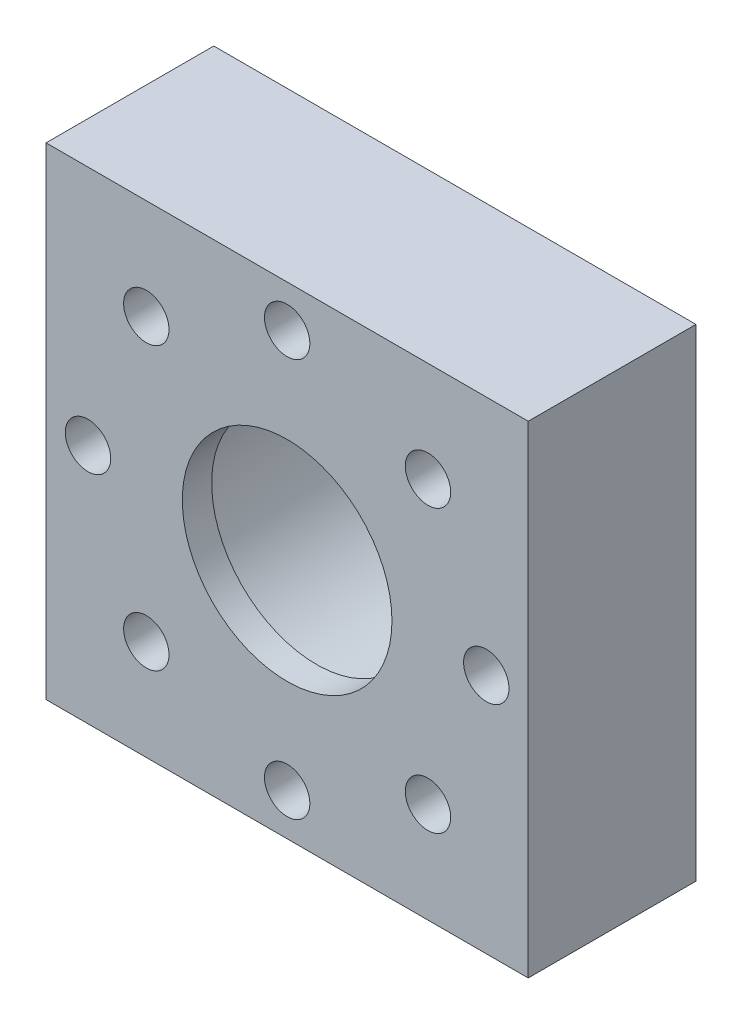
SolidWorks part; units mm, degrees
ref_plane "Front Plane" through (0, 0, 0) normal (0, 0, 1) x (1, 0, 0)
ref_plane "Top Plane" through (0, 0, 0) normal (0, 1, 0) x (1, 0, 0)
ref_plane "Right Plane" through (0, 0, 0) normal (1, 0, 0) x (0, 0, -1)
sketch "Sketch1" plane through (0, 0, 0) normal (0, 0, 1) x (1, 0, 0)
  line L0 (0, 0) -> (29.21, 0) construction
  line L1 (-29.21, -29.21) -> (29.21, -29.21)
  line L2 (-29.21, -29.21) -> (-29.21, 29.21)
  line L3 (-29.21, 29.21) -> (29.21, 29.21)
  line L4 (29.21, -29.21) -> (29.21, 29.21)
  line L5 (0, 0) -> (0, 29.21) construction
  dimension "D1" = 58.42
extrude "Boss-Extrude1" add sketch "Sketch1" along normal blind 20.32
sketch "Sketch5" plane through (0, 0, 0) normal (0, 0, -1) x (-1, 0, 0)
  point P0 (0, 0)
sketch "Sketch6" plane through (0, 0, 0) normal (0, 0, -1) x (-1, 0, 0)
  circle A0 centre (0, 0) radius 29.21 construction
  circle A1 centre (0, 0) radius 24.13 construction
  point P5 (0, 24.13)
  dimension "D1" = 58.42
  dimension "D2" = 5.08
hole_wizard "1 NPT Tapped Hole2" positions "Sketch5" profile "Sketch7" size "1" standard "ANSI Inch" end condition up to next
sketch "Sketch7" plane through (0, 0, 0) normal (1, 0, 0) x (0, 1, 0)
  line L0 (0, 0) -> (0, 20.32)
  line L1 (0, 20.32) -> (14.4907, 20.32)
  line L2 (-15.228, 16.764) -> (-15.7299, 0) construction
  line L3 (14.4907, 20.32) -> (14.4907, 16.764)
  line L4 (14.4907, 16.764) -> (15.228, 16.764)
  line L5 (15.228, 16.764) -> (15.7299, 0)
  line L7 (15.7299, 0) -> (0, 0)
  line L8 (0, -6.35) -> (0, 107.95) construction
  line L11 (-14.4907, 16.764) -> (-15.228, 16.764) construction
  dimension "Thru Tap Drill Dia." = 28.9814
  dimension "Thru Tap Drill Depth" = 20.32
  dimension "Thread Dia." = 31.4598
  dimension "Thread Angle" = 3.43
  dimension "Thread Depth" = 16.764
cosmetic thread "Hole Thread1" parameters "D1"=16.764, "D2"=33.3996
hole_wizard "M5 Clearance Hole1" positions "Sketch6" profile "Sketch8" hole size "M5" standard "ANSI Metric" end condition up to next
sketch "Sketch8" plane through (0, 24.13, 0) normal (1, 0, 0) x (0, 1, 0)
  line L0 (0, 0) -> (0, 20.32)
  line L1 (0, 20.32) -> (2.75, 20.32)
  line L2 (2.75, 20.32) -> (2.75, 0)
  line L5 (2.75, 0) -> (0, 0)
  line L11 (0, -6.35) -> (0, 107.95) construction
  dimension "Thru Hole Dia." = 5.5
  dimension "Thru Hole Depth" = 20.32
pattern_circular "CirPattern1" count 8 every 45 about axis through (0, 0, 0) along (0, 0, 1) of "M5 Clearance Hole1"
sketch "Sketch9" plane through (0, 0, 20.32) normal (0, 0, 1) x (1, 0, 0)
  circle A0 centre (0, 0) radius 12.7
  circle A1 centre (0, 0) radius 14.4907 construction
  circle A2 centre (0, 0) radius 14.4907
  dimension "D1" = 25.4
extrude "Boss-Extrude2" add sketch "Sketch9" against normal up to surface (3.556 mm away) up to face at (-14.4907, 0, 16.764)
equation "\"le\"=2.43593"
equation "\"Cavity_Depth\" = 0.031in"
equation "\"Cavity_Width\" = 0.031in"
equation "\"Tooth_Width\" = .01in"
equation "\"Shaft_Seal_OD\"= 17mm'diameter at seal area"
equation "\"Shaft_clearance\"= .002in"
equation "\"O-Ring_ID\"= .801in"
equation "\"O-Ring_CS\"= .070in"
equation "\"Shaft_OD\"= .5in"
equation "\"Flange_OD\"=2.3in"
equation "\"D1@Sketch1\"=\"Flange_OD\""
equation "\"fitting_OD\"= 1.3in"
equation "\"plate_thick\"= .8in"
equation "\"D1@Boss-Extrude1\"=\"plate_thick\""
equation "\"D1@Sketch6\"=\"Flange_OD\""
